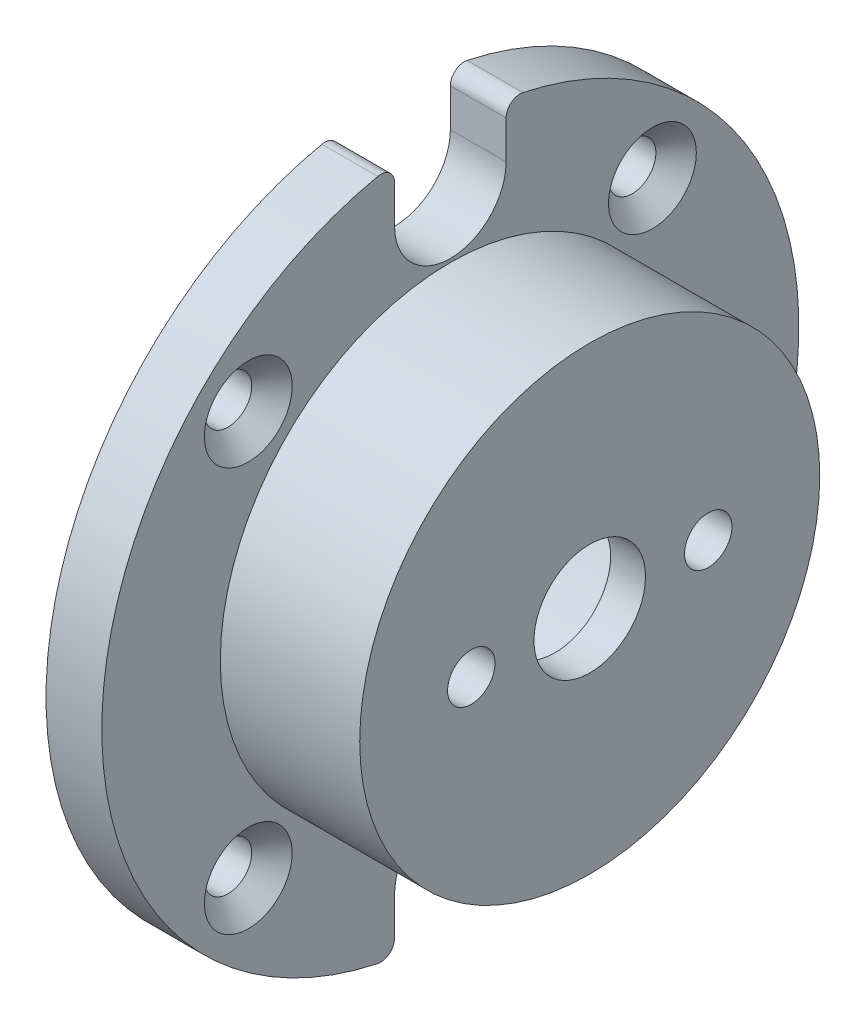
SolidWorks part; units mm, degrees
material "ABS"
ref_plane "Front Plane" through (0, 0, 0) normal (0, 0, 1) x (1, 0, 0)
ref_plane "Top Plane" through (0, 0, 0) normal (0, 1, 0) x (1, 0, 0)
ref_plane "Right Plane" through (0, 0, 0) normal (1, 0, 0) x (0, 0, -1)
sketch "Sketch1" plane through (0, 0, 0) normal (1, 0, 0) x (0, 0, -1)
  circle A0 centre (0, 0) radius 25
extrude "Boss-Extrude1" add sketch "Sketch1" along normal blind 4
sketch "Sketch2" plane through (4, 0, 0) normal (1, 0, 0) x (0, 0, -1)
  circle A0 centre (0, 0) radius 16.5
extrude "Boss-Extrude2" add sketch "Sketch2" along normal blind 10
sketch "Sketch3" plane through (0, 0, 0) normal (-1, 0, 0) x (0, 0, 1)
  circle A0 centre (0, 0) radius 12.5
extrude "Cut-Extrude1" cut sketch "Sketch3" against normal offset from surface (11.5 mm away) 2.5 up to face at (14, 0, -16.5)
sketch "Sketch4" plane through (14, 0, 0) normal (1, 0, 0) x (0, 0, -1)
  circle A0 centre (0, 0) radius 4
extrude "Cut-Extrude2" cut sketch "Sketch4" against normal blind 4
hole_wizard "M3 Clearance Hole1" positions "Sketch6" profile "Sketch5" hole size "M3" standard "ANSI Metric"
sketch "Sketch6" plane through (14, 0, 0) normal (1, 0, 0) x (0, 0, -1)
  point P0 (8.5, 0)
  point P2 (-8.5, 0)
  dimension "D1" = 8.5
  dimension "D2" = 8.5
sketch "Sketch5" plane through (14, 0, -8.5) normal (0, 1, 0) x (0, 0, -1)
  line L0 (0, 0) -> (0, 10)
  line L1 (0, 10) -> (1.7, 10)
  line L2 (1.7, 10) -> (1.7, 0)
  line L5 (1.7, 0) -> (0, 0)
  line L10 (0, 10) -> (-1.7, 10) construction
  line L11 (0, -6.35) -> (0, 107.95) construction
  dimension "Hole Dia." = 3.4
  dimension "Hole Depth" = 10
  dimension "Drill Angle" = 180
sketch "Sketch7" plane through (4, 0, 0) normal (1, 0, 0) x (0, 0, -1)
  line L0 (0, 0) -> (-14.4957, -14.4957) construction
hole_wizard "CSK for M3 Flat Head Machine Screw1" positions "Sketch9" profile "Sketch8" countersink size "M3" standard "ANSI Metric" end condition through all
sketch "Sketch9" plane through (4, 0, 0) normal (1, 0, 0) x (0, 0, -1)
  point P0 (-14.4957, -14.4957)
sketch "Sketch8" plane through (4, -14.4957, 14.4957) normal (0, 1, 0) x (0, 0, -1)
  line L0 (0, 0) -> (0, 4)
  line L1 (0, 4) -> (1.7, 4)
  line L2 (1.7, 4) -> (1.7, 1.45)
  line L3 (1.7, 1.45) -> (3.15, 0)
  line L5 (3.15, 0) -> (0, 0)
  line L6 (-1.7, 1.45) -> (-3.15, 0) construction
  line L11 (0, -6.35) -> (0, 107.95) construction
  dimension "Thru Hole Dia." = 3.4
  dimension "Thru Hole Depth" = 4
  dimension "Near C'Sink Dia." = 6.3
  dimension "Near C'Sink Angle" = 90
pattern_circular "CirPattern1" count 4 over 360 about axis through (0, 0, 0) along (1, 0, 0) of "CSK for M3 Flat Head Machine Screw1"
sketch "Sketch10" plane through (0, 0, 0) normal (-1, 0, 0) x (0, 0, 1)
  circle A0 centre (0, 0) radius 13.125
extrude "Cut-Extrude3" cut sketch "Sketch10" against normal up to surface (11.5 mm away) up to face at (11.5, 0, -10.2)
sketch "Sketch12" plane through (4, 0, 0) normal (1, 0, 0) x (0, 0, -1)
  line L0 (0, 16.5) -> (0, 25) construction
  line L1 (-4, 20.75) -> (-4, 23.4734)
  line L2 (4, 20.75) -> (4, 23.4734)
  line L3 (0, 0) -> (25, 0) construction
  line L4 (0, -16.5) -> (0, -25) construction
  line L5 (4, -20.75) -> (4, -23.4734)
  line L6 (-4, -20.75) -> (-4, -23.4734)
  circle A0 centre (0, 0) radius 16.5 construction
  circle A1 centre (0, 0) radius 25 construction
  arc A2 (-4, 20.75) -> (4, 20.75) centre (0, 20.75) ccw
  arc A3 (5.2083, 24.4514) -> (-5.2083, 24.4514) centre (0, 0) ccw
  arc A4 (4, 23.4734) -> (5.2083, 24.4514) centre (5, 23.4734) cw
  arc A5 (-4, 23.4734) -> (-5.2083, 24.4514) centre (-5, 23.4734) ccw
  arc A6 (-4, -23.4734) -> (-5.2083, -24.4514) centre (-5, -23.4734) cw
  arc A7 (4, -23.4734) -> (5.2083, -24.4514) centre (5, -23.4734) ccw
  arc A8 (5.2083, -24.4514) -> (-5.2083, -24.4514) centre (0, 0) cw
  arc A9 (-4, -20.75) -> (4, -20.75) centre (0, -20.75) cw
  point P16 (4, 24.6779)
  point P19 (-4, 24.6779)
  point P33 (-4, -24.6779)
  point P34 (4, -24.6779)
  dimension "D1" = 1
extrude "Cut-Extrude4" cut sketch "Sketch12" against normal blind 10
